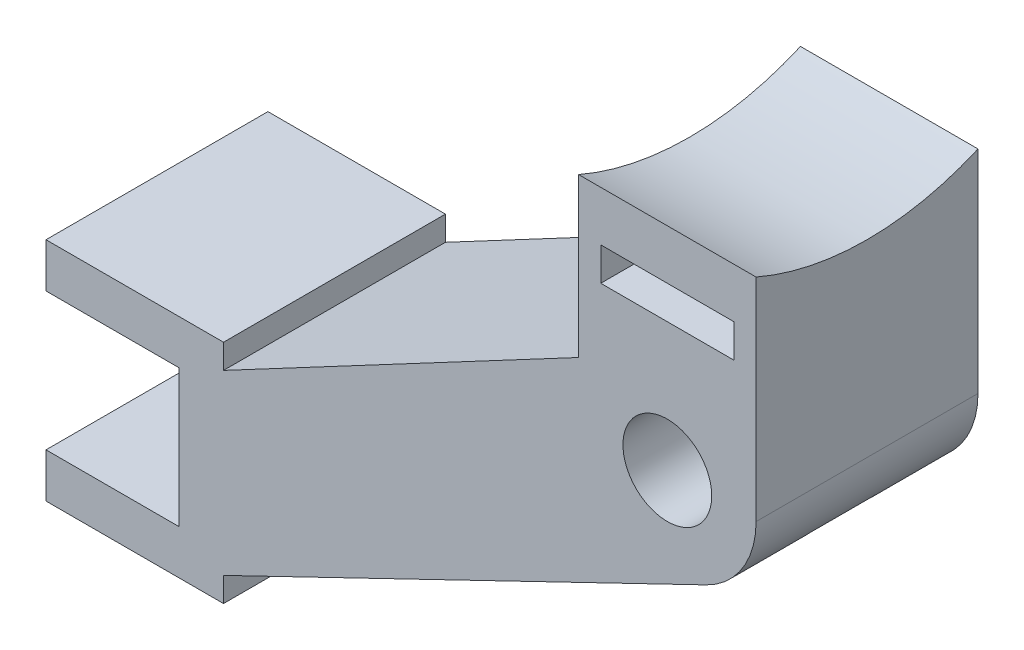
SolidWorks part; units mm, degrees
ref_plane "Plano frontal" through (0, 0, 0) normal (0, 0, 1) x (1, 0, 0)
ref_plane "Plano superior" through (0, 0, 0) normal (0, 1, 0) x (1, 0, 0)
ref_plane "Plano direito" through (0, 0, 0) normal (1, 0, 0) x (0, 0, -1)
sketch "Esboço1" plane through (0, 0, 0) normal (0, 0, 1) x (1, 0, 0)
  line L0 (0, 0) -> (-22, 0) construction
  line L1 (-22, 0) -> (-22, -10.1) construction
  line L2 (-28, -7) -> (-22, -7)
  line L3 (-22, -7) -> (-22, -13.2)
  line L4 (-22, -13.2) -> (-28, -13.2)
  line L5 (-28, -13.2) -> (-28, -15.2)
  line L6 (-28, -15.2) -> (-20, -15.2)
  line L7 (-20, -14.1) -> (1.7394, -3.602)
  line L8 (-28, -7) -> (-28, -5)
  line L9 (-28, -5) -> (-20, -5)
  line L10 (-20, -5) -> (-20, -6.1)
  line L11 (-20, -6.1) -> (-4, 2.4039)
  line L12 (-20, -15.2) -> (-20, -14.1)
  line L13 (0, 0.1928) -> (0, 1.0879) construction
  line L14 (-4, 8) -> (4, 8)
  line L15 (4, 8) -> (4, 0)
  line L17 (-4, 2.4039) -> (-4, 8)
  line L18 (0, 8) -> (0, 3.8906) construction
  line L19 (-3, 7.3) -> (3, 7.3)
  line L20 (-3, 7.3) -> (-3, 5.8)
  line L21 (-3, 5.8) -> (3, 5.8)
  line L22 (3, 7.3) -> (3, 5.8)
  line L23 (-3, 7.3) -> (3, 5.8) construction
  line L24 (-3, 5.8) -> (3, 7.3) construction
  circle A0 centre (0, 0) radius 2
  arc A1 (1.7394, -3.602) -> (4, 0) centre (0, 0) ccw
  point P17 (-22, -10.1)
  point P18 (0, 3.6252)
  point P22 (0, 8)
  point P27 (0, 3.6814)
  point P28 (0, 6.55)
  point P33 (0, 5)
  point P34 (0, 3.7363)
  dimension "D1" = 4
  dimension "D2" = 8
  dimension "D3" = 22
  dimension "D4" = 10.1
  dimension "D5" = 6.2
  dimension "D6" = 2
  dimension "D7" = 8
  dimension "D8" = 8
  dimension "D9" = 6
  dimension "D10" = 8
  dimension "D11" = 8
  dimension "D12" = 8
  dimension "D13" = 6
  dimension "D14" = 1.5
  dimension "D15" = 0.7
extrude "Ressalto-extrusão1" add sketch "Esboço1" along normal blind 10
sketch "Esboço2" plane through (0, 0, 0) normal (1, 0, 0) x (0, 0, -1)
  line L0 (-5, 8.5) -> (-5, 22.8272) construction
  line L2 (-5, 8.5) -> (-5, -3.602) construction
  line L3 (0, -3.602) -> (0, 0) construction
  line L4 (0, 8) -> (0, 9.5436)
  line L5 (-10, -3.602) -> (0, -3.602) construction
  line L6 (-10, 9.5436) -> (-10, 8)
  line L8 (-10, 8) -> (0, 8)
  arc A0 (-10, 9.5436) -> (0, 9.5436) centre (-5, 21) ccw
  point P1 (-5, 18.2719)
  point P11 (-5, 8.5)
  dimension "D1" = 25
  dimension "D2" = 13
extrude "Ressalto-extrusão4" add sketch "Esboço2" along normal up to surface (8 mm away) from vertex at -4 contours A0 L6 L8 L4 up to face at (4, 4, 5) starting at point (-4, 8, 10)
sketch "Esboço3" plane through (0, 0, 0) normal (0, 1, 0) x (1, 0, 0)
  line L0 (4, -10) -> (4, 0) construction
  line L2 (-3, -3.5) -> (3, -3.5)
  line L3 (-3, -3.5) -> (-3, -6.5)
  line L4 (-3, -6.5) -> (3, -6.5)
  line L5 (3, -3.5) -> (3, -6.5)
  line L6 (-3, -3.5) -> (3, -6.5) construction
  line L7 (-3, -6.5) -> (3, -3.5) construction
  point P0 (0, -5)
  point P6 (0, 0)
  point P8 (0, 0)
  point P11 (4, -5)
  dimension "D1" = 6
  dimension "D2" = 3
extrude "Corte-extrusão1" cut sketch "Esboço3" against normal up to next from offset 4 contours L5 L4 L3 L2
